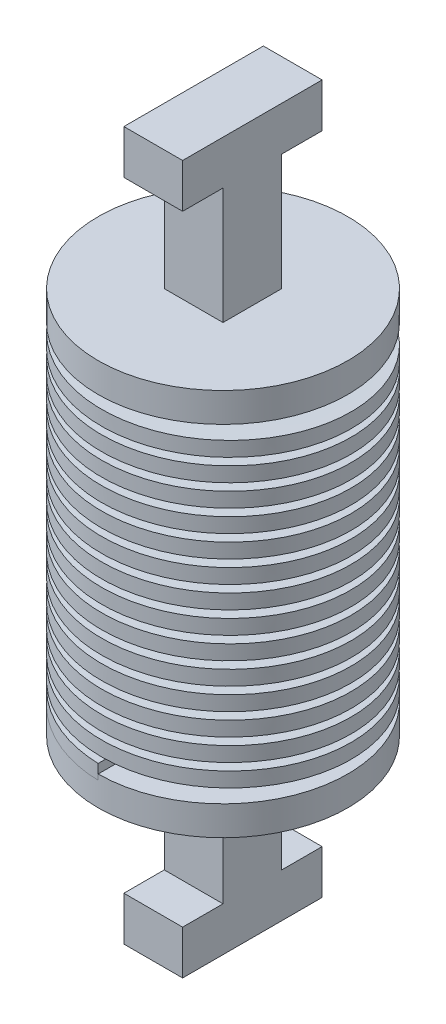
SolidWorks part; units mm, degrees
ref_plane "Front Plane" through (0, 0, 0) normal (0, 0, 1) x (1, 0, 0)
ref_plane "Top Plane" through (0, 0, 0) normal (0, 1, 0) x (1, 0, 0)
ref_plane "Right Plane" through (0, 0, 0) normal (1, 0, 0) x (0, 0, -1)
sketch "Sketch1" plane through (0, 0, 0) normal (0, 1, 0) x (1, 0, 0)
  circle A0 centre (0, 0) radius 7.5
curve "Helix/Spiral1" pitch 1.5 height 21.75 turns 14.5
sketch "Sketch4" plane through (0, 0, 0) normal (0, 0, 1) x (1, 0, 0)
  line L1 (-8.5, 1) -> (-4.5, 1)
  line L2 (-8.5, 1) -> (-8.5, 0)
  line L3 (-8.5, 0) -> (-4.5, 0)
  line L4 (-4.5, 1) -> (-4.5, 0)
  line L5 (-8.5, 1) -> (-4.5, 0) construction
  line L6 (-8.5, 0) -> (-4.5, 1) construction
  point P0 (-5.6693, 0.2923)
  dimension "D1" = 1
  dimension "D2" = 4
sweep "Sweep1" add profiles "Sketch4" path "Helix/Spiral1"
sketch "Sketch5" plane through (0, 0, 0) normal (0, 1, 0) x (1, 0, 0)
  circle A0 centre (0, 0) radius 8.5
extrude "Boss-Extrude1" add sketch "Sketch5" against normal blind 2
sketch3d "3DSketch4"
  circle A0 centre (0, 22.375, 0) radius 8.5
  point P3 (0, 30.875, 0)
sketch "Sketch9" plane through (0, 22.375, 0) normal (0, 1, 0) x (1, 0, 0)
  circle A0 centre (0, 0) radius 8.5
extrude "Boss-Extrude8" add sketch "Sketch9" along normal blind 2 separate body
sketch "Sketch13" plane through (0, 24.375, 0) normal (0, 1, 0) x (1, 0, 0)
  line L1 (-2, -2) -> (2, -2)
  line L2 (-2, -2) -> (-2, 2)
  line L3 (-2, 2) -> (2, 2)
  line L4 (2, -2) -> (2, 2)
  line L5 (-2, -2) -> (2, 2) construction
  line L6 (-2, 2) -> (2, -2) construction
  point P0 (0, 0)
  dimension "D1" = 4
  dimension "D2" = 4
sketch "Sketch15" plane through (0, -2, 0) normal (0, -1, 0) x (1, 0, 0)
  line L1 (-2, -2) -> (2, -2)
  line L2 (-2, -2) -> (-2, 2)
  line L3 (-2, 2) -> (2, 2)
  line L4 (2, -2) -> (2, 2)
  line L5 (-2, -2) -> (2, 2) construction
  line L6 (-2, 2) -> (2, -2) construction
  point P0 (0, 0)
  dimension "D1" = 4
  dimension "D2" = 4
extrude "Boss-Extrude14" add sketch "Sketch13" along normal blind 8
sketch "Sketch18" plane through (-2, 0, 0) normal (-1, 0, 0) x (0, 0, 1)
  line L0 (-2, 32.375) -> (-2, 24.375) construction
  line L1 (-4.75, 32.3087) -> (4.75, 32.3087)
  line L2 (-4.75, 32.3087) -> (-4.75, 35.3087)
  line L3 (-4.75, 35.3087) -> (4.75, 35.3087)
  line L4 (4.75, 32.3087) -> (4.75, 35.3087)
  dimension "D1" = 9.5
  dimension "D2" = 3
  dimension "D3" = 2.75
extrude "Boss-Extrude15" add sketch "Sketch18" against normal blind 4 contours L2 L1 L4 L3
extrude "Boss-Extrude16" add sketch "Sketch15" along normal blind 8
sketch "Sketch19" plane through (-2, 0, 0) normal (-1, 0, 0) x (0, 0, 1)
  line L0 (-2, -10) -> (-2, -2) construction
  line L1 (-4.75, -9.9055) -> (4.75, -9.9055)
  line L2 (-4.75, -9.9055) -> (-4.75, -12.9055)
  line L3 (-4.75, -12.9055) -> (4.75, -12.9055)
  line L4 (4.75, -9.9055) -> (4.75, -12.9055)
  dimension "D1" = 2.75
  dimension "D2" = 9.5
  dimension "D3" = 3
extrude "Boss-Extrude17" add sketch "Sketch19" against normal blind 4
